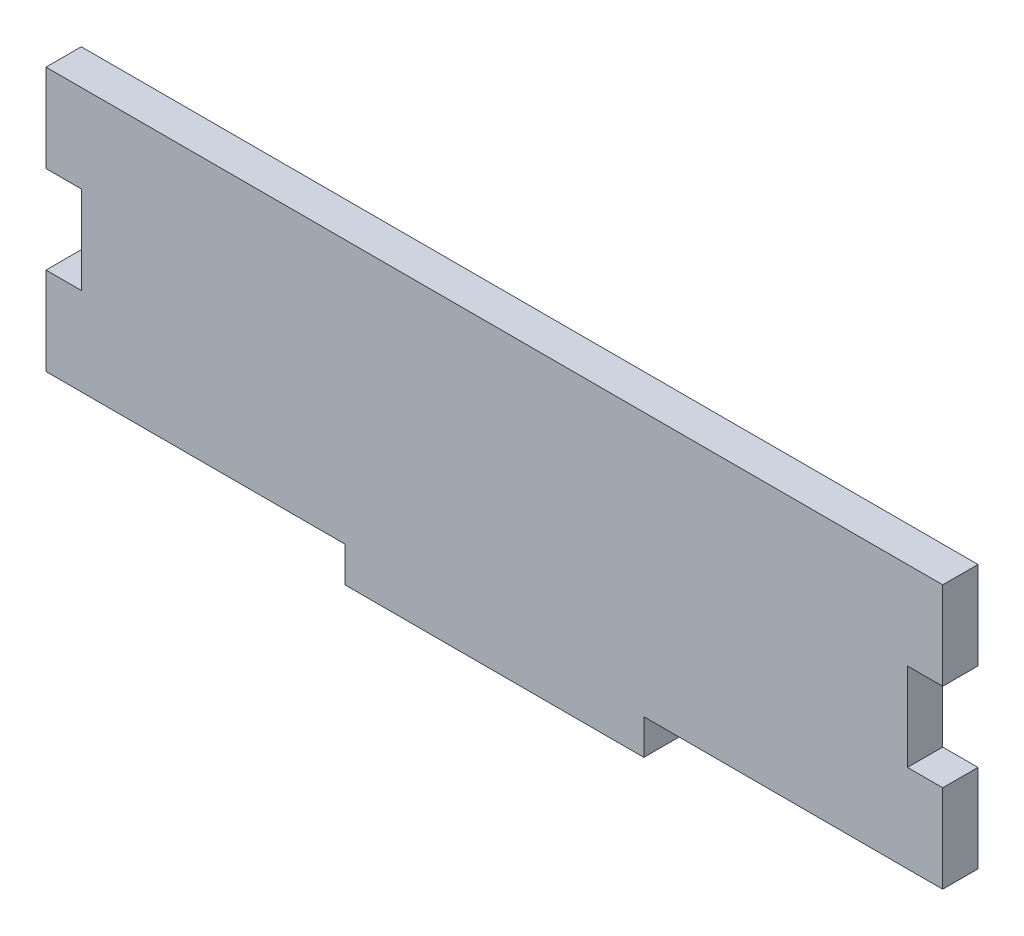
SolidWorks part; units mm, degrees
ref_plane "Front Plane" through (0, 0, 0) normal (0, 0, 1) x (1, 0, 0)
ref_plane "Top Plane" through (0, 0, 0) normal (0, 1, 0) x (1, 0, 0)
ref_plane "Right Plane" through (0, 0, 0) normal (1, 0, 0) x (0, 0, -1)
sketch "Sketch1" plane through (0, 0, 0) normal (0, 0, 1) x (1, 0, 0)
  line L0 (-15.3558, 18.8529) -> (-15.3558, 26.3205)
  line L1 (10.0442, 0.9205) -> (35.4442, 0.9205)
  line L2 (-15.3558, 3.9177) -> (-15.3558, 11.3853)
  line L3 (-15.3558, 26.3205) -> (60.8442, 26.3205)
  line L4 (60.8442, 3.9177) -> (60.8442, 11.3853)
  line L5 (-15.3558, 18.8529) -> (-12.3586, 18.8529)
  line L6 (60.8442, 18.8529) -> (60.8442, 26.3205)
  line L7 (-15.3558, 3.9177) -> (10.0442, 3.9177)
  line L8 (10.0442, 0.9205) -> (10.0442, 3.9177)
  line L9 (-15.3558, 11.3853) -> (-12.3586, 11.3853)
  line L10 (-12.3586, 18.8529) -> (-12.3586, 11.3853)
  line L11 (60.8442, 3.9177) -> (35.4442, 3.9177)
  line L12 (35.4442, 0.9205) -> (35.4442, 3.9177)
  line L13 (60.8442, 18.8529) -> (57.847, 18.8529)
  line L15 (60.8442, 11.3853) -> (57.847, 11.3853)
  line L16 (57.847, 18.8529) -> (57.847, 11.3853)
  dimension "width" = 76.2
  dimension "height" = 25.4
  dimension "thick" = 2.9972
extrude "Boss-Extrude1" add sketch "Sketch1" along normal blind 2.9972
